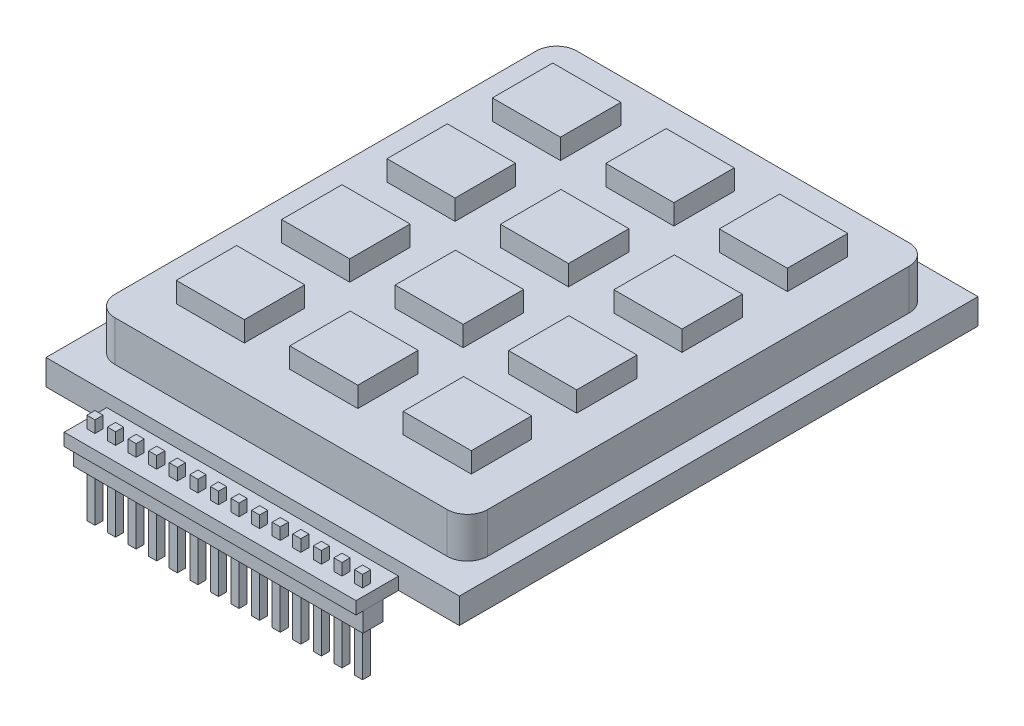
SolidWorks part; units mm, degrees
ref_plane "Plan de face" through (0, 0, 0) normal (0, 0, 1) x (1, 0, 0)
ref_plane "Plan de dessus" through (0, 0, 0) normal (0, 1, 0) x (1, 0, 0)
ref_plane "Plan de droite" through (0, 0, 0) normal (1, 0, 0) x (0, 0, -1)
sketch "Esquisse1" plane through (0, 0, 0) normal (0, 1, 0) x (1, 0, 0)
  line L1 (0, 0) -> (51, 0)
  line L2 (0, 0) -> (0, 64)
  line L3 (0, 64) -> (51, 64)
  line L4 (51, 0) -> (51, 64)
  dimension "D1" = 64
  dimension "D2" = 51
extrude "Boss.-Extru.1" add sketch "Esquisse1" along normal blind 3.15
sketch "Esquisse2" plane through (0, 3.15, 0) normal (0, 1, 0) x (1, 0, 0)
  line L4 (0, 32) -> (2.5, 32) construction
  line L5 (0, 64) -> (0, 0) construction
  line L6 (25.5, 3.5) -> (25.5, 0) construction
  line L7 (0, 0) -> (51, 0) construction
  line L12 (2.5, 58) -> (2.5, 6)
  line L13 (5, 3.5) -> (46, 3.5)
  line L14 (48.5, 6) -> (48.5, 58)
  line L15 (46, 60.5) -> (5, 60.5)
  arc A0 (2.5, 6) -> (5, 3.5) centre (5, 6) ccw
  arc A1 (46, 3.5) -> (48.5, 6) centre (46, 6) ccw
  arc A2 (48.5, 58) -> (46, 60.5) centre (46, 58) ccw
  arc A3 (2.5, 58) -> (5, 60.5) centre (5, 58) cw
  point P14 (2.5, 3.5)
  point P19 (48.5, 60.5)
  point P22 (2.5, 60.5)
  dimension "D3" = 2.5
  dimension "D1" = 46
  dimension "D2" = 57
extrude "Boss.-Extru.2" add sketch "Esquisse2" along normal blind 5
sketch "Esquisse3" plane through (0, 8.15, 0) normal (0, 1, 0) x (1, 0, 0)
  line L0 (25.5, 60.5) -> (25.5, 3.5) construction
  line L1 (46, 60.5) -> (5, 60.5) construction
  line L2 (5, 3.5) -> (46, 3.5) construction
  line L3 (2.5, 51.5) -> (48.5, 51.5) construction
  line L4 (2.5, 58) -> (2.5, 6) construction
  line L5 (48.5, 6) -> (48.5, 58) construction
  line L6 (39.5, 60.5) -> (39.5, 3.5) construction
  line L7 (2.5, 38.5) -> (48.5, 38.5) construction
  line L8 (46, 60.5) -> (5, 60.5) construction
  line L9 (2.5, 58) -> (2.5, 6) construction
  line L10 (2.5, 25.5) -> (48.5, 25.5) construction
  line L11 (5, 3.5) -> (46, 3.5) construction
  line L12 (2.5, 12.5) -> (48.5, 12.5) construction
  line L13 (48.5, 6) -> (48.5, 58) construction
  line L14 (7.3, 42.225) -> (15.7, 42.225)
  line L15 (11.5, 60.5) -> (11.5, 3.5) construction
  line L16 (7.3, 55.225) -> (15.7, 55.225)
  line L17 (7.3, 55.225) -> (7.3, 47.775)
  line L18 (7.3, 47.775) -> (15.7, 47.775)
  line L19 (15.7, 55.225) -> (15.7, 47.775)
  line L20 (7.3, 55.225) -> (15.7, 47.775) construction
  line L21 (7.3, 47.775) -> (15.7, 55.225) construction
  line L22 (21.3, 55.225) -> (29.7, 55.225)
  line L23 (21.3, 55.225) -> (21.3, 47.775)
  line L24 (21.3, 47.775) -> (29.7, 47.775)
  line L25 (29.7, 55.225) -> (29.7, 47.775)
  line L26 (21.3, 55.225) -> (29.7, 47.775) construction
  line L27 (21.3, 47.775) -> (29.7, 55.225) construction
  line L28 (35.3, 55.225) -> (43.7, 55.225)
  line L29 (35.3, 55.225) -> (35.3, 47.775)
  line L30 (35.3, 47.775) -> (43.7, 47.775)
  line L31 (43.7, 55.225) -> (43.7, 47.775)
  line L32 (35.3, 55.225) -> (43.7, 47.775) construction
  line L33 (35.3, 47.775) -> (43.7, 55.225) construction
  line L34 (7.3, 42.225) -> (7.3, 34.775)
  line L35 (7.3, 34.775) -> (15.7, 34.775)
  line L36 (15.7, 42.225) -> (15.7, 34.775)
  line L37 (7.3, 42.225) -> (15.7, 34.775) construction
  line L38 (7.3, 34.775) -> (15.7, 42.225) construction
  line L39 (21.3, 42.225) -> (29.7, 42.225)
  line L40 (21.3, 42.225) -> (21.3, 34.775)
  line L41 (21.3, 34.775) -> (29.7, 34.775)
  line L42 (29.7, 42.225) -> (29.7, 34.775)
  line L43 (21.3, 42.225) -> (29.7, 34.775) construction
  line L44 (21.3, 34.775) -> (29.7, 42.225) construction
  line L45 (35.3, 42.225) -> (43.7, 42.225)
  line L46 (35.3, 42.225) -> (35.3, 34.775)
  line L47 (35.3, 34.775) -> (43.7, 34.775)
  line L48 (43.7, 42.225) -> (43.7, 34.775)
  line L49 (35.3, 42.225) -> (43.7, 34.775) construction
  line L50 (35.3, 34.775) -> (43.7, 42.225) construction
  line L51 (7.3, 16.225) -> (15.7, 16.225)
  line L52 (7.3, 29.225) -> (15.7, 29.225)
  line L53 (7.3, 29.225) -> (7.3, 21.775)
  line L54 (7.3, 21.775) -> (15.7, 21.775)
  line L55 (15.7, 29.225) -> (15.7, 21.775)
  line L56 (7.3, 29.225) -> (15.7, 21.775) construction
  line L57 (7.3, 21.775) -> (15.7, 29.225) construction
  line L58 (21.3, 29.225) -> (29.7, 29.225)
  line L59 (21.3, 29.225) -> (21.3, 21.775)
  line L60 (21.3, 21.775) -> (29.7, 21.775)
  line L61 (29.7, 29.225) -> (29.7, 21.775)
  line L62 (21.3, 29.225) -> (29.7, 21.775) construction
  line L63 (21.3, 21.775) -> (29.7, 29.225) construction
  line L64 (35.3, 29.225) -> (43.7, 29.225)
  line L65 (35.3, 29.225) -> (35.3, 21.775)
  line L66 (35.3, 21.775) -> (43.7, 21.775)
  line L67 (43.7, 29.225) -> (43.7, 21.775)
  line L68 (35.3, 29.225) -> (43.7, 21.775) construction
  line L69 (35.3, 21.775) -> (43.7, 29.225) construction
  line L70 (7.3, 16.225) -> (7.3, 8.775)
  line L71 (7.3, 8.775) -> (15.7, 8.775)
  line L72 (15.7, 16.225) -> (15.7, 8.775)
  line L73 (7.3, 16.225) -> (15.7, 8.775) construction
  line L74 (7.3, 8.775) -> (15.7, 16.225) construction
  line L75 (21.3, 16.225) -> (29.7, 16.225)
  line L76 (21.3, 16.225) -> (21.3, 8.775)
  line L77 (21.3, 8.775) -> (29.7, 8.775)
  line L78 (29.7, 16.225) -> (29.7, 8.775)
  line L79 (21.3, 16.225) -> (29.7, 8.775) construction
  line L80 (21.3, 8.775) -> (29.7, 16.225) construction
  line L81 (35.3, 16.225) -> (43.7, 16.225)
  line L82 (35.3, 16.225) -> (35.3, 8.775)
  line L83 (35.3, 8.775) -> (43.7, 8.775)
  line L84 (43.7, 16.225) -> (43.7, 8.775)
  line L85 (35.3, 16.225) -> (43.7, 8.775) construction
  line L86 (35.3, 8.775) -> (43.7, 16.225) construction
  point P30 (11.5, 51.5)
  point P35 (25.5, 51.5)
  point P40 (39.5, 51.5)
  point P45 (11.5, 51.5)
  point P46 (39.5, 51.5)
  point P47 (11.5, 38.5)
  point P52 (25.5, 38.5)
  point P57 (39.5, 38.5)
  point P62 (39.5, 38.5)
  point P63 (25.5, 38.5)
  point P64 (11.5, 38.5)
  point P65 (43.7, 34.3172)
  point P66 (39.5, 38.5)
  point P67 (11.5, 38.5)
  point P68 (43.7, 34.775)
  point P69 (11.5, 25.5)
  point P74 (25.5, 25.5)
  point P79 (39.5, 25.5)
  point P84 (11.5, 12.5)
  point P89 (25.5, 12.5)
  point P94 (39.5, 12.5)
  point P99 (11.5, 25.5)
  point P100 (24.9401, 25.5)
  point P101 (39.5, 25.5)
  point P102 (25.5, 25.5)
  point P103 (11.5, 12.5)
  point P104 (25.5, 12.5)
  point P105 (39.5, 12.5)
  dimension "D1" = 13
  dimension "D2" = 13
  dimension "D3" = 13
  dimension "D4" = 9
  dimension "D5" = 14
  dimension "D6" = 14
  dimension "D7" = 8.4
  dimension "D8" = 7.45
extrude "Boss.-Extru.3" add sketch "Esquisse3" along normal blind 2.5
sketch "Esquisse4" plane through (0, 0, 0) normal (0, -1, 0) x (1, 0, 0)
  line L0 (7.5, 0) -> (7.5, 5.25)
  line L1 (0, 0) -> (51, 0) construction
  line L2 (7.5, 5.25) -> (43.5, 5.25)
  line L3 (43.5, 5.25) -> (43.5, 0)
  line L6 (7.5, 0) -> (43.5, 0)
  point P6 (25.5, 0)
  point P7 (25.5, 0)
  dimension "D1" = 36
  dimension "D3" = 5.25
extrude "Boss.-Extru.4" add sketch "Esquisse4" against normal blind 1.54
sketch "Esquisse5" plane through (0, 0, 0) normal (0, -1, 0) x (1, 0, 0)
  line L0 (25.5, 5.25) -> (25.5, -12.9737) construction
  line L1 (43.5, 5.25) -> (7.5, 5.25) construction
  line L3 (43.36, 1.75) -> (7.64, 1.75)
  line L4 (43.36, 1.75) -> (43.36, 4.25)
  line L5 (43.36, 4.25) -> (7.64, 4.25)
  line L6 (7.64, 1.75) -> (7.64, 4.25)
  line L7 (43.36, 1.75) -> (7.64, 4.25) construction
  line L8 (43.36, 4.25) -> (7.64, 1.75) construction
  point P4 (25.5, 3)
  dimension "D1" = 35.72
  dimension "D2" = 2.5
  dimension "D3" = 1
extrude "Boss.-Extru.5" add sketch "Esquisse5" along normal blind 2.52
sketch "Esquisse6" plane through (0, -2.52, 0) normal (0, -1, 0) x (1, 0, 0)
  line L0 (7.64, 3) -> (43.36, 3) construction
  line L1 (8.5415, 3.5) -> (9.5415, 3.5)
  line L2 (8.5415, 3.5) -> (8.5415, 2.5)
  line L3 (8.5415, 2.5) -> (9.5415, 2.5)
  line L4 (9.5415, 3.5) -> (9.5415, 2.5)
  line L5 (8.5415, 3.5) -> (9.5415, 2.5) construction
  line L6 (8.5415, 2.5) -> (9.5415, 3.5) construction
  line L7 (7.64, 4.25) -> (7.64, 1.75) construction
  line L8 (43.36, 1.75) -> (43.36, 4.25) construction
  line L9 (11.0815, 3.5) -> (12.0815, 3.5)
  line L10 (11.0815, 3.5) -> (11.0815, 2.5)
  line L11 (12.0815, 3.5) -> (12.0815, 2.5)
  line L12 (11.0815, 2.5) -> (12.0815, 2.5)
  line L13 (11.0815, 3.5) -> (12.0815, 2.5) construction
  line L14 (11.0815, 2.5) -> (12.0815, 3.5) construction
  line L15 (13.6215, 3.5) -> (14.6215, 3.5)
  line L16 (13.6215, 3.5) -> (13.6215, 2.5)
  line L17 (14.6215, 3.5) -> (14.6215, 2.5)
  line L18 (13.6215, 2.5) -> (14.6215, 2.5)
  line L19 (13.6215, 3.5) -> (14.6215, 2.5) construction
  line L20 (13.6215, 2.5) -> (14.6215, 3.5) construction
  line L21 (16.1615, 3.5) -> (17.1615, 3.5)
  line L22 (16.1615, 3.5) -> (16.1615, 2.5)
  line L23 (17.1615, 3.5) -> (17.1615, 2.5)
  line L24 (16.1615, 2.5) -> (17.1615, 2.5)
  line L25 (16.1615, 3.5) -> (17.1615, 2.5) construction
  line L26 (16.1615, 2.5) -> (17.1615, 3.5) construction
  line L27 (18.7015, 3.5) -> (19.7015, 3.5)
  line L28 (18.7015, 3.5) -> (18.7015, 2.5)
  line L29 (19.7015, 3.5) -> (19.7015, 2.5)
  line L30 (18.7015, 2.5) -> (19.7015, 2.5)
  line L31 (18.7015, 3.5) -> (19.7015, 2.5) construction
  line L32 (18.7015, 2.5) -> (19.7015, 3.5) construction
  line L33 (21.2415, 3.5) -> (22.2415, 3.5)
  line L34 (21.2415, 3.5) -> (21.2415, 2.5)
  line L35 (22.2415, 3.5) -> (22.2415, 2.5)
  line L36 (21.2415, 2.5) -> (22.2415, 2.5)
  line L37 (21.2415, 3.5) -> (22.2415, 2.5) construction
  line L38 (21.2415, 2.5) -> (22.2415, 3.5) construction
  line L39 (23.7815, 3.5) -> (24.7815, 3.5)
  line L40 (23.7815, 3.5) -> (23.7815, 2.5)
  line L41 (24.7815, 3.5) -> (24.7815, 2.5)
  line L42 (23.7815, 2.5) -> (24.7815, 2.5)
  line L43 (23.7815, 3.5) -> (24.7815, 2.5) construction
  line L44 (23.7815, 2.5) -> (24.7815, 3.5) construction
  line L45 (26.3215, 3.5) -> (27.3215, 3.5)
  line L46 (26.3215, 3.5) -> (26.3215, 2.5)
  line L47 (27.3215, 3.5) -> (27.3215, 2.5)
  line L48 (26.3215, 2.5) -> (27.3215, 2.5)
  line L49 (26.3215, 3.5) -> (27.3215, 2.5) construction
  line L50 (26.3215, 2.5) -> (27.3215, 3.5) construction
  line L51 (28.8615, 3.5) -> (29.8615, 3.5)
  line L52 (28.8615, 3.5) -> (28.8615, 2.5)
  line L53 (29.8615, 3.5) -> (29.8615, 2.5)
  line L54 (28.8615, 2.5) -> (29.8615, 2.5)
  line L55 (28.8615, 3.5) -> (29.8615, 2.5) construction
  line L56 (28.8615, 2.5) -> (29.8615, 3.5) construction
  line L57 (31.4015, 3.5) -> (32.4015, 3.5)
  line L58 (31.4015, 3.5) -> (31.4015, 2.5)
  line L59 (32.4015, 3.5) -> (32.4015, 2.5)
  line L60 (31.4015, 2.5) -> (32.4015, 2.5)
  line L61 (31.4015, 3.5) -> (32.4015, 2.5) construction
  line L62 (31.4015, 2.5) -> (32.4015, 3.5) construction
  line L63 (33.9415, 3.5) -> (34.9415, 3.5)
  line L64 (33.9415, 3.5) -> (33.9415, 2.5)
  line L65 (34.9415, 3.5) -> (34.9415, 2.5)
  line L66 (33.9415, 2.5) -> (34.9415, 2.5)
  line L67 (33.9415, 3.5) -> (34.9415, 2.5) construction
  line L68 (33.9415, 2.5) -> (34.9415, 3.5) construction
  line L69 (36.4815, 3.5) -> (37.4815, 3.5)
  line L70 (36.4815, 3.5) -> (36.4815, 2.5)
  line L71 (37.4815, 3.5) -> (37.4815, 2.5)
  line L72 (36.4815, 2.5) -> (37.4815, 2.5)
  line L73 (36.4815, 3.5) -> (37.4815, 2.5) construction
  line L74 (36.4815, 2.5) -> (37.4815, 3.5) construction
  line L75 (39.0215, 3.5) -> (40.0215, 3.5)
  line L76 (39.0215, 3.5) -> (39.0215, 2.5)
  line L77 (40.0215, 3.5) -> (40.0215, 2.5)
  line L78 (39.0215, 2.5) -> (40.0215, 2.5)
  line L79 (39.0215, 3.5) -> (40.0215, 2.5) construction
  line L80 (39.0215, 2.5) -> (40.0215, 3.5) construction
  line L81 (41.5615, 3.5) -> (42.5615, 3.5)
  line L82 (41.5615, 3.5) -> (41.5615, 2.5)
  line L83 (42.5615, 3.5) -> (42.5615, 2.5)
  line L84 (41.5615, 2.5) -> (42.5615, 2.5)
  line L85 (41.5615, 3.5) -> (42.5615, 2.5) construction
  line L86 (41.5615, 2.5) -> (42.5615, 3.5) construction
  point P0 (9.0415, 3)
  dimension "D1" = 0.9015
  dimension "D2" = 1
  dimension "D3" = 14
extrude "Boss.-Extru.6" add sketch "Esquisse6" along normal blind 5.75 and the other way blind 5.52
